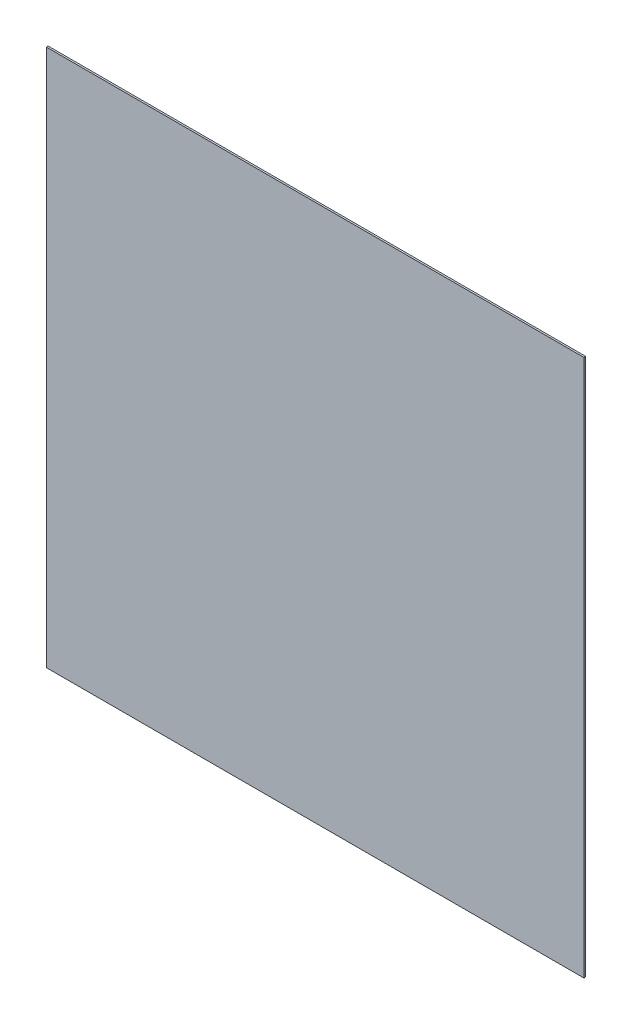
SolidWorks part; units mm, degrees
ref_plane "前视基准面" through (0, 0, 0) normal (0, 0, 1) x (1, 0, 0)
ref_plane "上视基准面" through (0, 0, 0) normal (0, 1, 0) x (1, 0, 0)
ref_plane "右视基准面" through (0, 0, 0) normal (1, 0, 0) x (0, 0, -1)
sketch "草图1" plane through (0, 0, 0) normal (0, 0, 1) x (1, 0, 0)
  line L1 (0, 0) -> (300, 0)
  line L2 (0, 0) -> (0, 300)
  line L3 (0, 300) -> (300, 300)
  line L4 (300, 0) -> (300, 300)
  dimension "D1" = 300
  dimension "D2" = 300
extrude "凸台-拉伸1" add sketch "草图1" along normal blind 1
